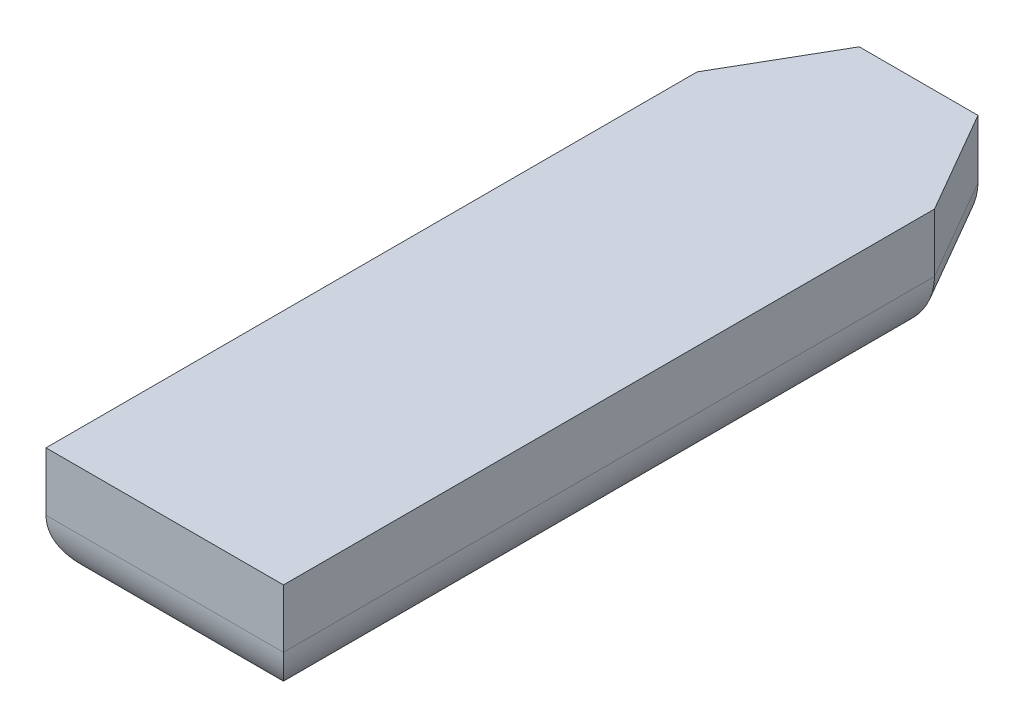
SolidWorks part; units mm, degrees
ref_plane "Front Plane" through (0, 0, 0) normal (0, 0, 1) x (1, 0, 0)
ref_plane "Top Plane" through (0, 0, 0) normal (0, 1, 0) x (1, 0, 0)
ref_plane "Right Plane" through (0, 0, 0) normal (1, 0, 0) x (0, 0, -1)
sketch "Sketch1" plane through (0, 0, 0) normal (0, 1, 0) x (1, 0, 0)
  line L0 (10, -27.4199) -> (10, 27.4199)
  line L2 (-10, 27.4199) -> (-10, -27.4199)
  line L3 (-10, -27.4199) -> (10, -27.4199)
  line L5 (-5, 36.0801) -> (5, 36.0801)
  line L6 (10, 27.4199) -> (5, 36.0801)
  line L7 (-5, 36.0801) -> (-10, 27.4199)
  point P2 (0, -27.4199)
  point P10 (10, 23.8687)
  point P11 (10, 23.3864)
  point P12 (-10, 0)
  dimension "D1" = 120
  dimension "D2" = 63.5
  dimension "D3" = 20
  dimension "D4" = 120
  dimension "D5" = 10
extrude "Boss-Extrude1" add sketch "Sketch1" along normal blind 10
fillet "Fillet1" radius 5.08 6 edges at (10, 0, 0) (-10, 0, 0) (0, 0, 27.4199) (0, 0, -36.0801) (7.5, 0, -31.75) (-7.5, 0, -31.75)
